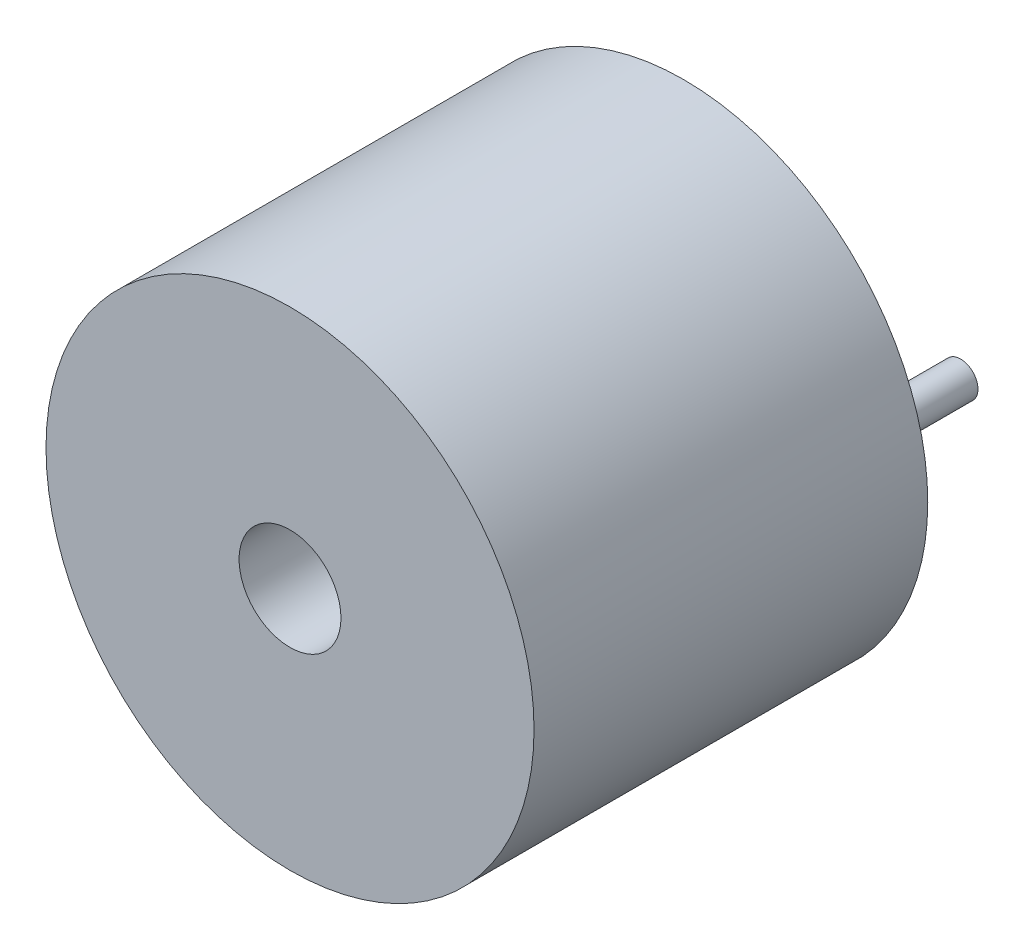
SolidWorks part; units mm, degrees
ref_plane "Front Plane" through (0, 0, 0) normal (0, 0, 1) x (1, 0, 0)
ref_plane "Top Plane" through (0, 0, 0) normal (0, 1, 0) x (1, 0, 0)
ref_plane "Right Plane" through (0, 0, 0) normal (1, 0, 0) x (0, 0, -1)
sketch "Sketch1" plane through (0, 0, 0) normal (0, 0, 1) x (1, 0, 0)
  circle A0 centre (0, 0) radius 5.95
  dimension "D1" = 11.9
extrude "Boss-Extrude1" add sketch "Sketch1" along normal blind 9.6
sketch "Sketch2" plane through (0, 0, 9.6) normal (0, 0, 1) x (1, 0, 0)
  circle A0 centre (0, 0) radius 1.242
extrude "Cut-Extrude1" cut sketch "Sketch2" against normal blind 2
sketch "Sketch3" plane through (0, 0, 0) normal (0, 0, -1) x (-1, 0, 0)
  line L0 (-3.75, 0) -> (3.75, 0) construction
  circle A0 centre (-3.75, 0) radius 0.425
  circle A1 centre (3.75, 0) radius 0.425
  point P2 (0, 0)
  dimension "D2" = 0.85
  dimension "D1" = 7.5
extrude "Boss-Extrude2" add sketch "Sketch3" along normal blind 3
